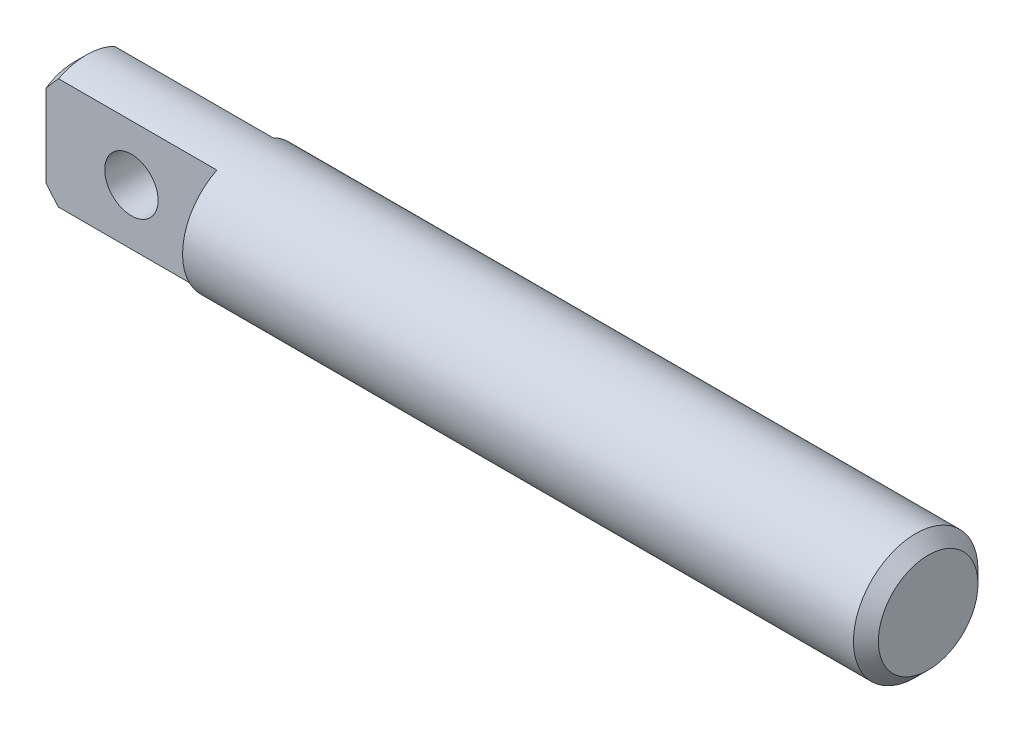
SolidWorks part; units mm, degrees
ref_plane "Front" through (0, 0, 0) normal (0, 0, 1) x (1, 0, 0)
ref_plane "Top" through (0, 0, 0) normal (0, 1, 0) x (1, 0, 0)
ref_plane "Right" through (0, 0, 0) normal (1, 0, 0) x (0, 0, -1)
sketch "Sketch1" plane through (0, 0, 0) normal (0, 0, 1) x (1, 0, 0)
  line L0 (-19.05, 0) -> (19.05, 0) construction
  line L1 (19.05, 2.7781) -> (19.05, -2.7781) construction
  line L2 (-19.05, 2.7781) -> (-19.05, -2.7781) construction
  dimension "Length" = 38.1
  dimension "Diameter" = 5.5562
sketch "Sketch2" plane through (0, 0, 0) normal (1, 0, 0) x (0, 0, -1)
  circle A0 centre (0, 0) radius 2.7781
extrude "Extrude1" add sketch "Sketch2" against normal up to vertex (19.05 mm away) and the other way up to vertex (19.05 mm away) up to point (-19.05, 2.7781, 0) other way up to point (19.05, 2.7781, 0)
chamfer "Chamfer1" distance 0.5556 angle 45 2 edges at (19.05, 0, -2.7781) (-19.05, 0, -2.7781)
sketch "Sketch3" plane through (-19.05, 0, 0) normal (-1, 0, 0) x (0, 0, 1)
  line L1 (-3.175, -3.175) -> (3.175, -3.175)
  line L2 (-3.175, -3.175) -> (-3.175, 3.175)
  line L3 (-3.175, 3.175) -> (3.175, 3.175)
  line L4 (3.175, -3.175) -> (3.175, 3.175)
  line L5 (-3.175, -3.175) -> (3.175, 3.175) construction
  line L6 (-3.175, 3.175) -> (3.175, -3.175) construction
  line L7 (-1.2502, -3.175) -> (1.2502, -3.175)
  line L8 (-1.2502, -3.175) -> (-1.2502, 3.175)
  line L9 (-1.2502, 3.175) -> (1.2502, 3.175)
  line L10 (1.2502, -3.175) -> (1.2502, 3.175)
  line L11 (-1.2502, -3.175) -> (1.2502, 3.175) construction
  line L12 (-1.2502, 3.175) -> (1.2502, -3.175) construction
  point P0 (0, 0)
  point P5 (0, 0)
  circle M9 centre (0, 0) radius 2.2225
  dimension "D1" = 6.35
  dimension "D2" = 6.35
  dimension "D3" = 2.5003
extrude "Cut-Extrude1" cut sketch "Sketch3" against normal blind 7.62 contours L1 L8 L3 L2 M9 | L10 L1 L4 L3 M9 | L8 M9 | L10 M9
sketch "Sketch5" plane through (0, 0, 1.2502) normal (0, 0, 1) x (1, 0, 0)
  line L0 (-19.05, -1.8376) -> (-19.05, 1.8376) construction
  circle A0 centre (-15.24, 0) radius 1.1906
  point P4 (-19.05, 0)
  dimension "D1" = 2.3813
  dimension "D2" = 3.81
extrude "Cut-Extrude2" cut sketch "Sketch5" against normal through all
equation "\"D1@Chamfer1\" = \"Diameter@Sketch1\"*.1"
